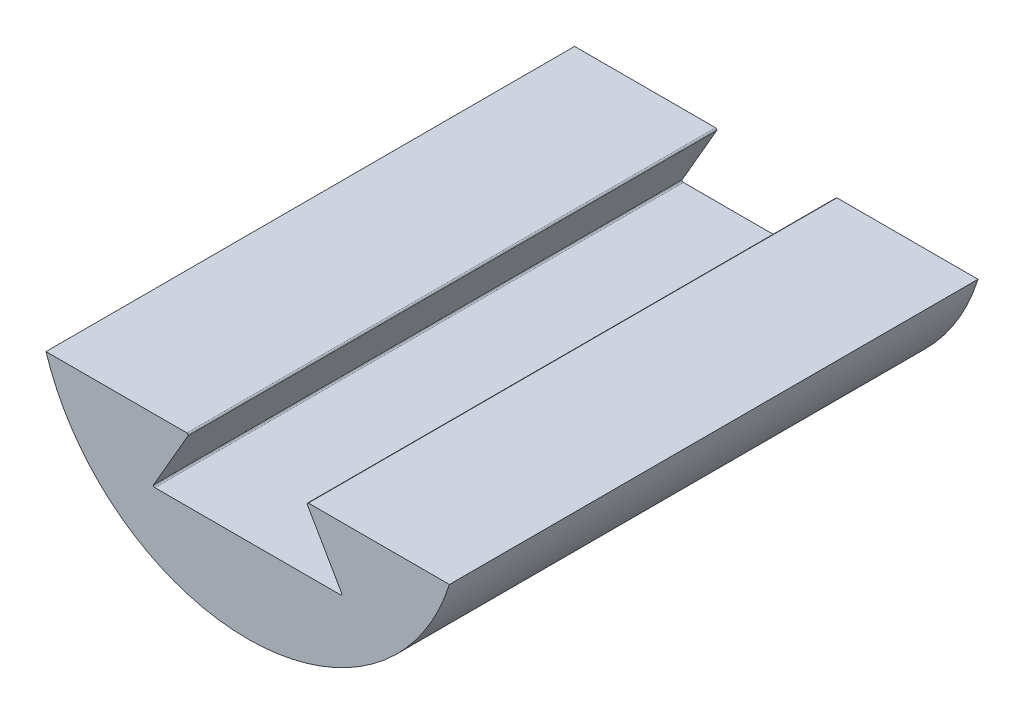
SolidWorks part; units mm, degrees
ref_plane "Front Plane" through (0, 0, 0) normal (0, 0, 1) x (1, 0, 0)
ref_plane "Top Plane" through (0, 0, 0) normal (0, 1, 0) x (1, 0, 0)
ref_plane "Right Plane" through (0, 0, 0) normal (1, 0, 0) x (0, 0, -1)
sketch "Sketch2" plane through (0, 0, 0) normal (0, 0, 1) x (1, 0, 0)
  line L0 (-38.1576, -12) -> (38.1576, -12)
  arc A0 (-38.1576, -12) -> (38.1576, -12) centre (0, 0) ccw
  dimension "D1" = 80
  dimension "D2" = 12
extrude "Boss-Extrude1" add sketch "Sketch2" along normal blind 100
sketch "Sketch3" plane through (0, 0, 0) normal (0, 0, -1) x (-1, 0, 0)
  line L0 (-11.0718, -12) -> (-18, -24)
  line L1 (-38.1576, -12) -> (38.1576, -12) construction
  line L2 (-18, -24) -> (18, -24)
  line L3 (18, -24) -> (11.0718, -12)
  line L4 (0, -12) -> (0, -24) construction
  line L8 (11.0718, -12) -> (-11.0718, -12)
  dimension "D1" = 60
  dimension "D2" = 60
  dimension "D3" = 12
  dimension "D4" = 36
extrude "Cut-Extrude1" cut sketch "Sketch3" against normal through all
fillet "Fillet1" radius 0.25 4 edges at (-18, -24, 50) (-11.0718, -12, 50) (18, -24, 50) (11.0718, -12, 50)
